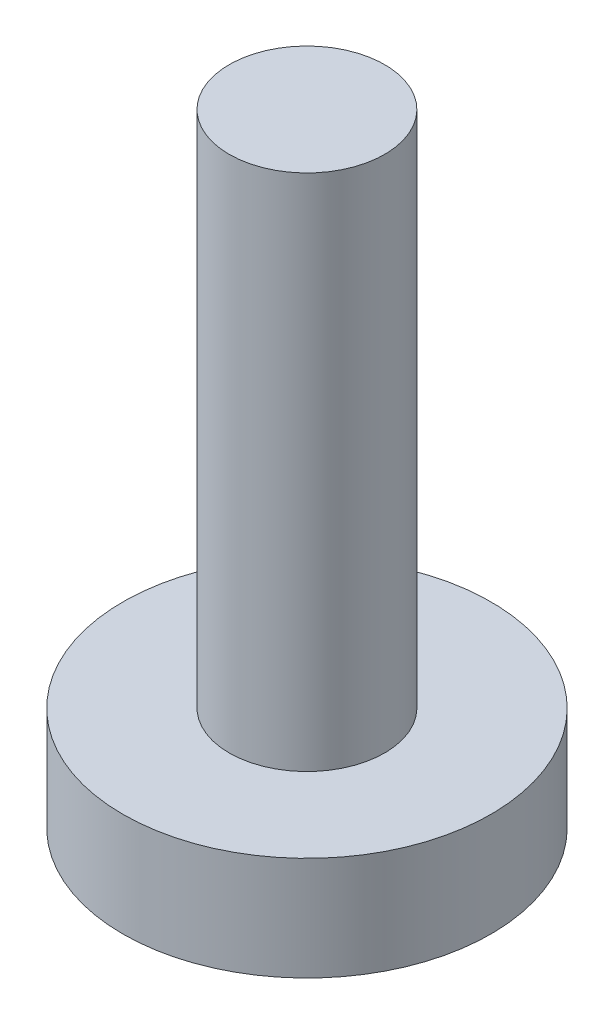
SolidWorks part; units mm, degrees
ref_plane "前视基准面" through (0, 0, 0) normal (0, 0, 1) x (1, 0, 0)
ref_plane "上视基准面" through (0, 0, 0) normal (0, 1, 0) x (1, 0, 0)
ref_plane "右视基准面" through (0, 0, 0) normal (1, 0, 0) x (0, 0, -1)
sketch "草图1" plane through (0, 0, 0) normal (0, 1, 0) x (1, 0, 0)
  circle A0 centre (0, 0) radius 3.55
  dimension "D1" = 7.1
extrude "凸台-拉伸1" add sketch "草图1" along normal blind 2
sketch "草图2" plane through (0, 2, 0) normal (0, 1, 0) x (1, 0, 0)
  circle A0 centre (0, 0) radius 1.5
  dimension "D1" = 3
extrude "凸台-拉伸2" add sketch "草图2" along normal blind 10
